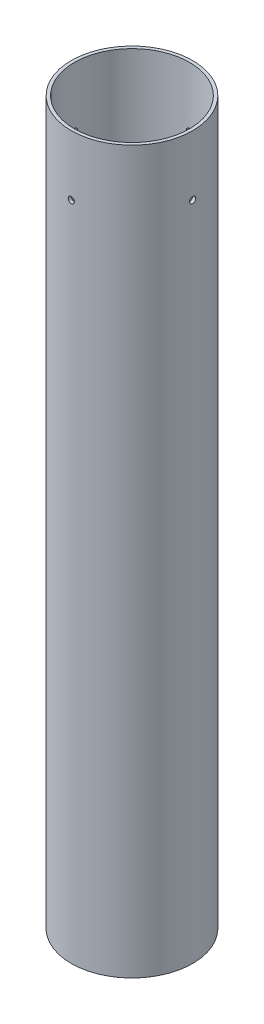
SolidWorks part; units mm, degrees
ref_plane "Front Plane" through (0, 0, 0) normal (0, 0, 1) x (1, 0, 0)
ref_plane "Top Plane" through (0, 0, 0) normal (0, 1, 0) x (1, 0, 0)
ref_plane "Right Plane" through (0, 0, 0) normal (1, 0, 0) x (0, 0, -1)
sketch "Sketch1" plane through (0, 0, 0) normal (0, 1, 0) x (1, 0, 0)
  circle A0 centre (0, 0) radius 36.5
  circle A1 centre (0, 0) radius 38.5
  dimension "D1" = 77
  dimension "D2" = 2
extrude "Boss-Extrude1" add sketch "Sketch1" along normal blind 457.2
sketch "Sketch2" plane through (0, 0, 0) normal (1, 0, 0) x (0, 0, -1)
  line L0 (0, 0) -> (0, 419.1) construction
  circle A0 centre (0, 419.1) radius 1.95
  dimension "D1" = 3.9
  dimension "D2" = 419.1
extrude "Cut-Extrude1" cut sketch "Sketch2" against normal through all both and the other way through all
sketch "Sketch3" plane through (0, 0, 0) normal (0, 0, 1) x (1, 0, 0)
  line L0 (0, 0) -> (0, 419.1) construction
  circle A0 centre (0, 419.1) radius 1.95
  dimension "D1" = 3.9
  dimension "D2" = 419.1
extrude "Cut-Extrude2" cut sketch "Sketch3" against normal through all both and the other way through all
